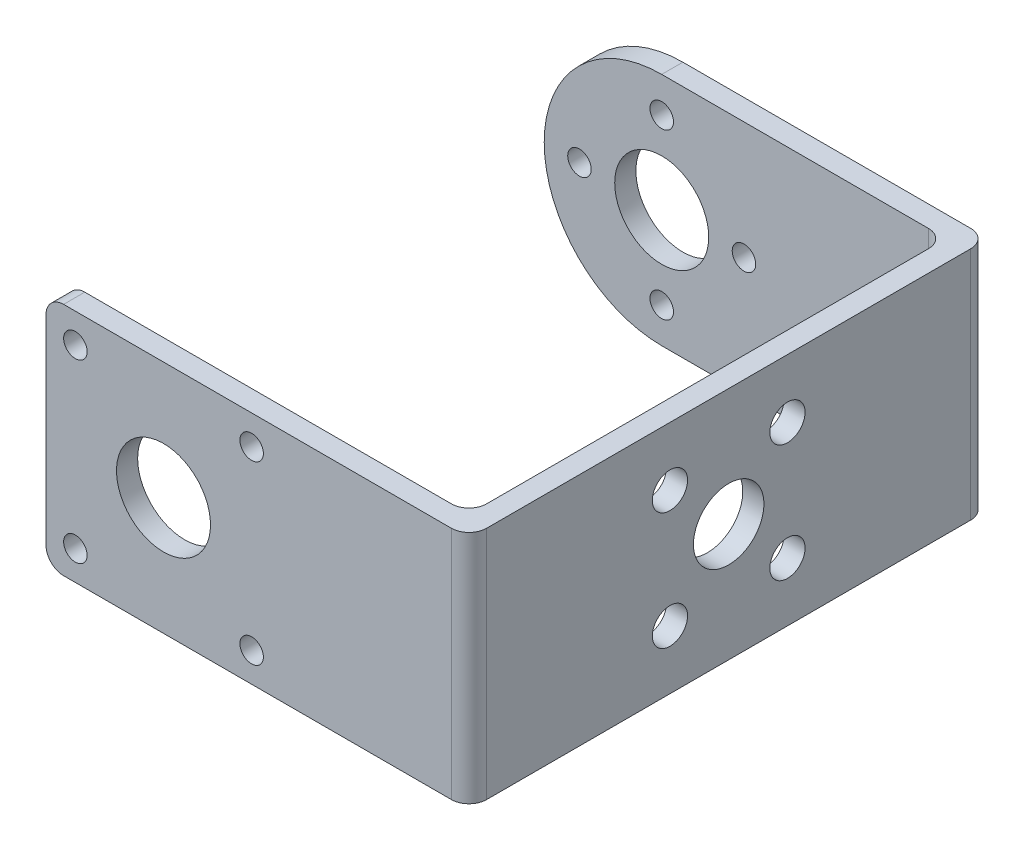
SolidWorks part; units mm, degrees
material "Beryllium"
ref_plane "Alzado" through (0, 0, 0) normal (0, 0, 1) x (1, 0, 0)
ref_plane "Planta" through (0, 0, 0) normal (0, 1, 0) x (1, 0, 0)
ref_plane "Vista lateral" through (0, 0, 0) normal (1, 0, 0) x (0, 0, -1)
sketch "Sketch1" plane through (0, 0, 0) normal (0, 1, 0) x (1, 0, 0)
  line L0 (-18, 20.3) -> (16.2, 20.3)
  line L1 (-18, -22.1) -> (18, -22.1)
  line L2 (-18, -22.1) -> (-18, 22.1) construction
  line L3 (-18, 22.1) -> (18, 22.1)
  line L4 (18, -22.1) -> (18, 22.1)
  line L5 (-18, -22.1) -> (18, 22.1) construction
  line L6 (-18, 22.1) -> (18, -22.1) construction
  line L7 (16.2, -20.3) -> (16.2, 20.3)
  line L8 (-18, -20.3) -> (16.2, -20.3)
  line L9 (-18, 22.1) -> (-18, 20.3)
  line L10 (-18, -20.3) -> (-18, -22.1)
  point P0 (0, 0)
  dimension "D1" = 36
  dimension "D2" = 44.2
  dimension "D3" = 1.8
extrude "Boss-Extrude1" add sketch "Sketch1" along normal mid plane 20 contours L3 L4 L1 L10 L8 L7 L0 L9
fillet "Fillet1" radius 1.5 6 edges at (16.2, 0, 20.3) (16.2, 0, -20.3) (-18, -10, 21.2) (-18, 10, 21.2) (18, 0, 22.1) (18, 0, -22.1)
sketch "Sketch2" plane through (0, 0, -22.1) normal (0, 0, -1) x (-1, 0, 0)
  line L0 (18, 10) -> (18, -10) construction
  line L1 (8, 10) -> (18, 10)
  line L3 (18, -10) -> (8, -10)
  line L4 (18, 10) -> (18, 0)
  line L5 (18, 0) -> (18, -10)
  arc A0 (8, -10) -> (8, 10) centre (8, 0) ccw
  line M2 (18, 10) -> (-16.5, 10)
  line M4 (-16.5, -10) -> (18, -10)
  line M5 (18, -10) -> (18, 10)
extrude "Cut-Extrude1" cut sketch "Sketch2" against normal blind 2 contours A0 M5 M2 | A0 M4 M5
sketch "Sketch4" plane through (0, 0, 22.1) normal (0, 0, 1) x (1, 0, 0)
  line L0 (-18, 8.5) -> (-18, -8.5) construction
  circle A0 centre (-8, 0) radius 4
  dimension "D1" = 8
  dimension "D2" = 10
extrude "Cut-Extrude3" cut sketch "Sketch4" against normal through all
sketch "Sketch6" plane through (16.2, 0, 0) normal (-1, 0, 0) x (0, 0, 1)
  line L0 (18.8, -10) -> (-18.8, -10) construction
  line L1 (-5, 5) -> (5, 5) construction
  line L2 (-5, 5) -> (-5, -5) construction
  line L3 (-5, -5) -> (5, -5) construction
  line L4 (5, 5) -> (5, -5) construction
  line L5 (-5, 5) -> (5, -5) construction
  line L6 (-5, -5) -> (5, 5) construction
  circle A0 centre (0, 0) radius 3
  circle A1 centre (5, -5) radius 1.5
  circle A2 centre (-5, -5) radius 1.5
  circle A3 centre (-5, 5) radius 1.5
  circle A4 centre (5, 5) radius 1.5
  point P19 (0, 0)
  dimension "D1" = 6
  dimension "D3" = 4
  dimension "D2" = 5
extrude "Cut-Extrude4" cut sketch "Sketch6" against normal blind 2
sketch "Sketch7" plane through (0, 0, 22.1) normal (0, 0, 1) x (1, 0, 0)
  line L0 (-18, 8.5) -> (-18, -8.5) construction
  line L1 (-0.5, 7.5) -> (-15.5, 7.5) construction
  line L2 (-0.5, 7.5) -> (-0.5, -7.5) construction
  line L3 (-0.5, -7.5) -> (-15.5, -7.5) construction
  line L4 (-15.5, 7.5) -> (-15.5, -7.5) construction
  line L5 (-0.5, 7.5) -> (-15.5, -7.5) construction
  line L6 (-0.5, -7.5) -> (-15.5, 7.5) construction
  circle A0 centre (-15.5, -7.5) radius 1
  circle A1 centre (-15.5, 7.5) radius 1
  circle A2 centre (-0.5, 7.5) radius 1
  circle A3 centre (-0.5, -7.5) radius 1
  point P0 (-8, 0)
  point P18 (-8, 0)
  dimension "D2" = 4
  dimension "D1" = 2.5
extrude "Cut-Extrude5" cut sketch "Sketch7" against normal blind 2
sketch "Sketch8" plane through (0, 0, -22.1) normal (0, 0, -1) x (-1, 0, 0)
  line L0 (8, 0) -> (8, -7) construction
  line L1 (8, -10) -> (-16.5, -10) construction
  circle A0 centre (8, -7) radius 1
  circle A1 centre (15, 0) radius 1
  circle A2 centre (8, 7) radius 1
  circle A3 centre (1, 0) radius 1
  point P15 (8, 0)
  dimension "D1" = 2
  dimension "D2" = 3
  dimension "D3" = 4
extrude "Cut-Extrude6" cut sketch "Sketch8" against normal blind 2
